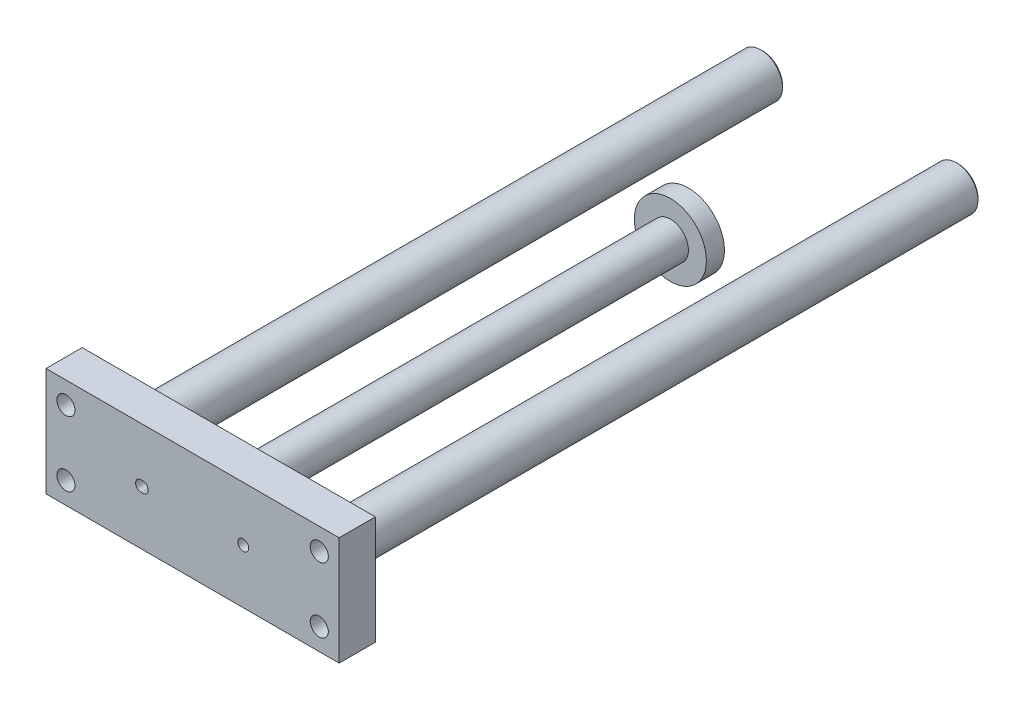
SolidWorks part; units mm, degrees
ref_plane "Plane1" through (0, 0, 0) normal (0, 0, 1) x (1, 0, 0)
ref_plane "Plane2" through (0, 0, 0) normal (0, 1, 0) x (1, 0, 0)
ref_plane "Plane3" through (0, 0, 0) normal (1, 0, 0) x (0, 0, -1)
sketch "Sketch1" plane through (0, 0, 0) normal (0, 0, 1) x (1, 0, 0)
  circle A0 centre (0, 0) radius 9.95
  dimension "D1" = 19.9
extrude "Piston" add sketch "Sketch1" along normal blind 5
sketch "Sketch2" plane through (0, 0, 0) normal (0, 0, 1) x (1, 0, 0)
  circle A0 centre (0, 0) radius 5
  dimension "D1" = 10
extrude "Rod" add sketch "Sketch2" along normal up to surface (127 mm away)
sketch "Sketch3" plane through (0, 0, 127) normal (0, 0, 1) x (1, 0, 0)
  line L0 (0, 0) -> (0, 3.9556) construction
  line L1 (-40.5, 15) -> (40.5, 15)
  line L2 (-40.5, 15) -> (-40.5, -15)
  line L3 (-40.5, -15) -> (40.5, -15)
  line L4 (40.5, 15) -> (40.5, -15)
  line L5 (0, 0) -> (3.9556, 0) construction
  dimension "D1" = 81
  dimension "D2" = 30
extrude "Plate" add sketch "Sketch3" along normal blind 10
sketch "Sketch4" plane through (0, 0, 127) normal (0, 0, -1) x (-1, 0, 0)
  line L0 (0, 0) -> (0, 19.638) construction
  circle A0 centre (-27, 0) radius 6
  circle A1 centre (27, 0) radius 6
  dimension "D1" = 12
  dimension "D2" = 54
extrude "Guides" add sketch "Sketch4" along normal up to surface (174.5 mm away)
sketch "Sketch5" plane through (0, 0, 137) normal (0, 0, 1) x (1, 0, 0)
  line L0 (0, 0) -> (0, 47.1532) construction
  circle A0 centre (14, 0) radius 1.5
  circle A1 centre (-14, 0) radius 1.5
  dimension "D1" = 3
  dimension "D2" = 28
extrude "MountHoles" cut sketch "Sketch5" against normal blind 6
chamfer "Chamfer1" distance 0.5 angle 45 2 edges at (21, 0, -47.5) (-33, 0, -47.5)
sketch "Sketch6" plane through (0, 0, 137) normal (0, 0, 1) x (1, 0, 0)
  line L0 (0, 0) -> (0, 55.313) construction
  line L1 (0, 0) -> (60.9143, 0) construction
  circle A0 centre (35, 9) radius 2.5
  circle A1 centre (-35, 9) radius 2.5
  circle A2 centre (35, -9) radius 2.5
  circle A3 centre (-35, -9) radius 2.5
  dimension "D3" = 18
  dimension "D4" = 9
extrude "MountHoles2" cut sketch "Sketch6" against normal through all
sketch "Sketch7" plane through (0, 0, 137) normal (0, 0, 1) x (1, 0, 0)
  line L0 (-14.25, 0) -> (-13.75, 0) construction
  line L1 (-14.25, 1.5) -> (-13.75, 1.5)
  line L2 (-14.25, -1.5) -> (-13.75, -1.5)
  arc A0 (-13.75, -1.5) -> (-13.75, 1.5) centre (-13.75, 0) ccw
  arc A1 (-14.25, 1.5) -> (-14.25, -1.5) centre (-14.25, 0) ccw
  circle A2 centre (-14, 0) radius 1.5 construction
  point P3 (-14, 0)
  dimension "D1" = 0.5
extrude "Cut-Extrude1X" cut sketch "Sketch7" against normal blind 3
